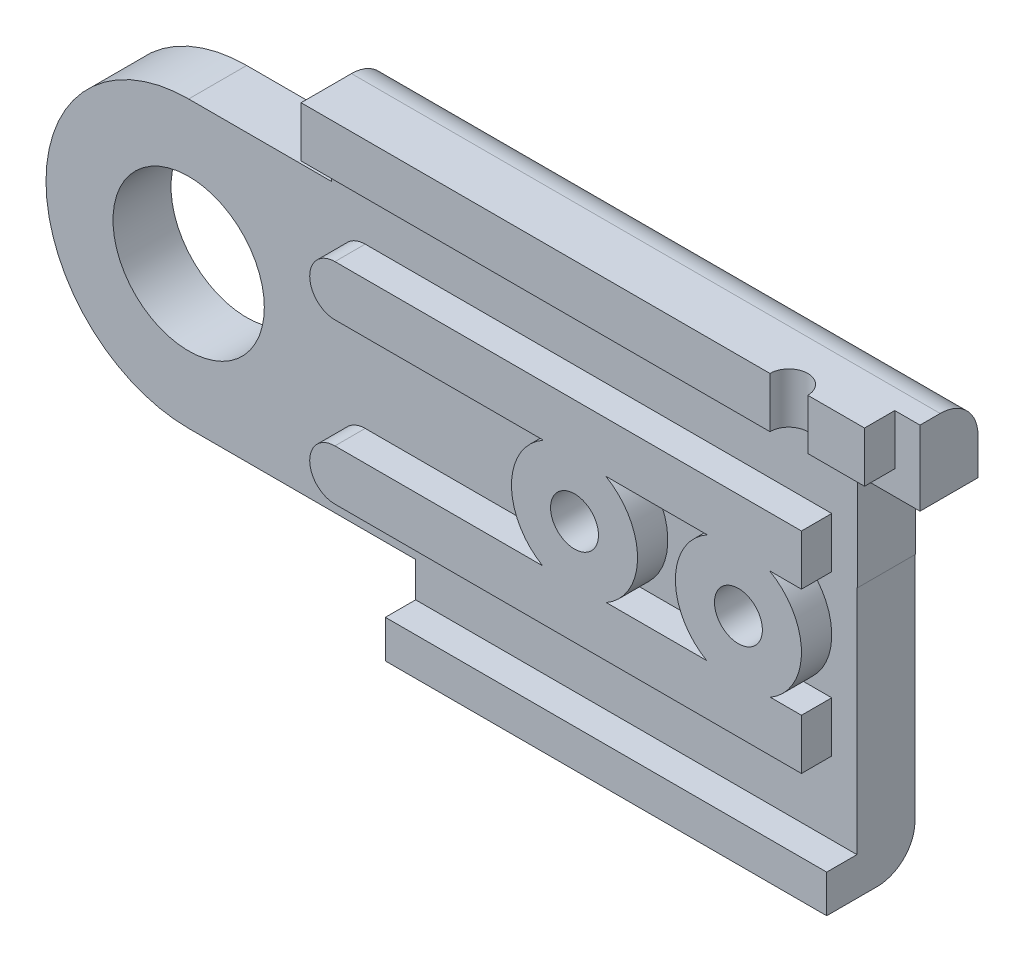
SolidWorks part; units mm, degrees
ref_plane "Front Plane" through (0, 0, 0) normal (0, 0, 1) x (1, 0, 0)
ref_plane "Top Plane" through (0, 0, 0) normal (0, 1, 0) x (1, 0, 0)
ref_plane "Right Plane" through (0, 0, 0) normal (1, 0, 0) x (0, 0, -1)
sketch "Sketch3" plane through (0, 0, 0) normal (0, 0, 1) x (1, 0, 0)
  line L7 (8, 0) -> (9, -2.5431)
  line L11 (35, 6.9569) -> (32, 7.4569)
  line L18 (5.6569, 5.6569) -> (5.6569, 7.4569)
  line L19 (5.6569, 7.4569) -> (32, 7.4569)
  line L20 (26.5, -7.0431) -> (9, -7.0431)
  line L21 (9, -7.0431) -> (9, -2.5431)
  line L23 (30.0502, -4.9929) -> (26.5, -7.0431)
  arc A4 (8, 0) -> (5.6569, 5.6569) centre (0, 0) ccw
  arc A5 (30.0502, -4.9929) -> (35, 6.9569) centre (35, -0.0431) ccw
  dimension "D3" = 3.5503
  dimension "D10" = 2.5431
  dimension "D17" = 14
  dimension "D4" = 5.6569
  dimension "D5" = 135
  dimension "D2" = 35
  dimension "D6" = 14.5
  dimension "D7" = 4.5
  dimension "D8" = 1
  dimension "D9" = 45
  dimension "D11" = 1.8
  dimension "D14" = 3
extrude "Boss-Extrude1" add sketch "Sketch3" along normal blind 2 contours A5 L11 L19 L18 A4 L7 L21 L20 L23
sketch "Sketch20" plane through (0, 0, 0) normal (0, 0, 1) x (1, 0, 0)
  line L0 (0, 7) -> (0, 7.5) construction
  line L1 (0, 7.5) -> (-19.4737, 7.5) construction
  line L2 (0, 5.3) -> (-14, 5.3) construction
  line L3 (0, 4) -> (-14, 4) construction
  line L4 (-14, 4) -> (-14, 5.3) construction
  line L5 (0, 5.3) -> (17.4849, 5.3) construction
  line L6 (17.4849, 5.3) -> (17.4849, 4) construction
  line L7 (17.4849, 4) -> (0, 4) construction
  line L8 (-2.5, 7.5) -> (-2.5, 2.868) construction
  circle A0 centre (0, 0) radius 7 construction
  circle A1 centre (0, 0) radius 3.9 construction
  circle A3 centre (0, 0) radius 5.3 construction
  circle A4 centre (0, 0) radius 4 construction
  circle A5 centre (0, 0) radius 2 construction
  dimension "D1" = 0
  dimension "D2" = 2.5
ref_plane "Plane1" through (0, 0, 2) normal (0, 0, 1) x (1, 0, 0)
sketch "Sketch4" plane through (0, 0, 2) normal (0, 0, 1) x (1, 0, 0)
  line L4 (5.6569, 5.6569) -> (5.6569, 7.5)
  line L5 (5.6569, 5.6569) -> (5.6569, 7.4569) construction
  line L6 (5.6569, 7.5) -> (26.5, 7.5)
  line L10 (8, 0) -> (9, -2.5431)
  line L11 (9, -2.5431) -> (9, -7.0431)
  line L12 (9, -7.0431) -> (26.5, -7.0431)
  line L13 (26.5, -7.0431) -> (26.5, 7.5)
  arc A0 (8, 0) -> (5.6569, 5.6569) centre (0, 0) ccw construction
  arc A3 (8, 0) -> (5.6569, 5.6569) centre (0, 0) ccw
sketch "Sketch22" plane through (0, 0, 2) normal (0, 0, 1) x (1, 0, 0)
  line L1 (5.6569, 7.4569) -> (26.5, 7.4569)
  line L6 (8, 0) -> (9, -2.5431)
  line L7 (9, -2.5431) -> (9, -7.0431)
  line L8 (9, -7.0431) -> (26.5, -7.0431)
  line L10 (26.5, 7.4569) -> (32, 7.4569)
  line L11 (32, 7.4569) -> (32, 2.1289)
  line L12 (32, 2.1289) -> (28.2751, 2.1289)
  line L13 (26.5, -7.0431) -> (28.2751, -6.018)
  line L14 (30.0502, -4.9929) -> (26.5, -7.0431) construction
  line L15 (28.2751, -6.018) -> (28.2751, 2.1289)
  line L16 (5.6569, 7.4569) -> (5.6569, 5.6569)
  arc A0 (8, 0) -> (5.6569, 5.6569) centre (0, 0) ccw
  dimension "D1" = 5.328
extrude "Boss-Extrude6" add sketch "Sketch22" along normal blind 4.5
sketch "Sketch25" plane through (0, 0, 2) normal (0, 0, 1) x (1, 0, 0)
  line L0 (0, 5.3) -> (18.0981, 5.3) construction
  line L1 (0, 4) -> (18.0981, 4) construction
  line L2 (18.0981, 4) -> (18.0981, 5.3) construction
sketch "Sketch26" plane through (0, 0, 2) normal (0, 0, 1) x (1, 0, 0)
  line L1 (18.0981, 5.3) -> (2.5301, 5.3)
  line L2 (18.0981, 4) -> (2.5301, 4)
  line L3 (2.5301, 5.3) -> (2.5301, 4)
  line L4 (18.0981, 5.3) -> (32, 5.3)
  line L5 (32, 2.1289) -> (32, 7.4569) construction
  line L6 (32, 5.3) -> (32, 4)
  line L7 (32, 4) -> (18.0981, 4)
extrude "Cut-Extrude6" cut sketch "Sketch26" along normal blind 4.5
ref_plane "Plane18" through (0, 0, 6.5) normal (0, 0, 1) x (1, 0, 0)
sketch "Sketch31" plane through (0, 0, 6.5) normal (0, 0, 1) x (1, 0, 0)
  line L0 (2.4327, 5.6569) -> (0, 5.6569)
  line L4 (9, -5.6569) -> (0, -5.6569)
  line L7 (2.4327, 5.6569) -> (5.6569, 5.6569)
  line L8 (5.6569, 5.6569) -> (5.6569, 7.4569)
  line L12 (9, -7.0431) -> (9, -5.6569)
  line L13 (9, -2.5431) -> (9, -7.0431) construction
  line L16 (32, 7.4569) -> (32, 2.1289)
  line L17 (32, 2.1289) -> (28.2751, 2.1289)
  line L22 (5.6569, 7.4569) -> (5.6569, 8.9569)
  line L23 (5.6569, 8.9569) -> (32, 8.9569)
  line L24 (32, 8.9569) -> (32, 7.4569)
  line L25 (9, -7.0431) -> (9, -8.5431)
  line L26 (9, -8.5431) -> (26.5, -8.5431)
  line L27 (26.5, -8.5431) -> (26.5, -7.0431)
  line L28 (26.5, -7.0431) -> (26.5, 2.1289)
  line L29 (26.5, 2.1289) -> (28.2751, 2.1289)
  line L30 (9, -7.0431) -> (26.5, -7.0431) construction
  line L31 (32, 7.4569) -> (5.6569, 7.4569) construction
  arc A0 (0, 5.6569) -> (0, -5.6569) centre (0, 0) ccw
  dimension "D1" = 5.6569
  dimension "D2" = 5.6569
  dimension "D3" = 1.5
  dimension "D4" = 1.5
extrude "Boss-Extrude14" add sketch "Sketch31" along normal blind 2.3 separate body
sketch "Sketch32" plane through (0, 0, 8.8) normal (0, 0, 1) x (1, 0, 0)
  circle A0 centre (0, 0) radius 3
  dimension "D1" = 6
extrude "Cut-Extrude7" cut sketch "Sketch32" against normal blind 2.3
sketch "Sketch33" plane through (0, 0, 8.8) normal (0, 0, 1) x (1, 0, 0)
  line L1 (5.6569, 8.9569) -> (5.6569, 6.9569)
  line L4 (9, -7.0431) -> (9, -8.5431)
  line L7 (7, -4.1569) -> (25.5, -4.1569)
  line L11 (9, -8.5431) -> (26.5, -8.5431)
  line L15 (26.5, -8.5431) -> (26.5, -7.0431)
  line L16 (26.5, -7.0431) -> (9, -7.0431)
  line L17 (5.6569, 8.9569) -> (28, 8.9569)
  line L18 (32, 8.9569) -> (5.6569, 8.9569) construction
  line L21 (28, 6.9569) -> (28, 8.9569)
  line L22 (25.5, -4.1569) -> (25.5, -2.1569)
  line L23 (25.5, -2.1569) -> (7, -2.1569)
  line L27 (5.6569, 6.9569) -> (28, 6.9569)
  line L28 (25.5, 2.172) -> (7, 2.172)
  line L30 (7, 4.172) -> (25.5, 4.172)
  line L33 (25.5, 2.172) -> (25.5, 4.172)
  line L34 (32, 2.1289) -> (32, 8.9569) construction
  line L35 (9, -8.5431) -> (26.5, -8.5431) construction
  line L37 (26.5, -8.5431) -> (26.5, 2.1289) construction
  arc A1 (7, -2.1569) -> (7, -4.1569) centre (7, -3.1569) ccw
  arc A2 (7, 4.172) -> (7, 2.172) centre (7, 3.172) ccw
  dimension "D1" = 1.5
  dimension "D2" = 2
  dimension "D3" = 2
  dimension "D5" = 2
  dimension "D6" = 2.5
  dimension "D8" = 4
extrude "Boss-Extrude15" add sketch "Sketch33" along normal blind 1.2
sketch "Sketch34" plane through (0, 0, 2) normal (0, 0, 1) x (1, 0, 0)
  line L0 (35, 5.3) -> (18.0981, 5.3) construction
  line L1 (35, 4) -> (18.0981, 4) construction
  circle A0 centre (35, -0.0431) radius 2 construction
  circle A1 centre (35, -0.0431) radius 5.3431 construction
  circle A2 centre (35, -0.0431) radius 4.0431 construction
sketch "Sketch35" plane through (0, 0, 8.8) normal (0, 0, 1) x (1, 0, 0)
  line L0 (32, 2.1289) -> (32, 6)
  line L1 (32, 2.1289) -> (26.5203, 2.1289)
  line L2 (32, 6) -> (26.5203, 6)
  line L3 (26.5203, 2.1289) -> (26.5203, 6)
  line L4 (32, 2.1289) -> (32, 8.9569) construction
  dimension "D1" = 5.4796
extrude "Cut-Extrude8" cut sketch "Sketch35" against normal blind 2.4
sketch "Sketch36" plane through (0, 0, 6.4) normal (0, 0, 1) x (1, 0, 0)
  line L0 (32, 2.1289) -> (32, 4)
  line L1 (32, 2.1289) -> (28.3, 2.1289)
  line L2 (32, 4) -> (28.3, 4)
  line L3 (28.3, 2.1289) -> (28.3, 4)
  line L4 (26.5, -7.0431) -> (26.5, 7.5) construction
  dimension "D1" = 1.8
extrude "Cut-Extrude9" cut sketch "Sketch36" against normal blind 4.4
sketch "Sketch37" plane through (0, 0, 2) normal (0, 0, 1) x (1, 0, 0)
  circle A0 centre (35, -0.0431) radius 3.9
  dimension "D1" = 7.8
extrude "Boss-Extrude16" add sketch "Sketch37" along normal blind 4.4
sketch "Sketch39" plane through (0, 0, 6.4) normal (0, 0, 1) x (1, 0, 0)
  line L0 (34, 0.9367) -> (34, -1.0229)
  arc A0 (34, -1.0229) -> (34, 0.9367) centre (35, -0.0431) ccw
  dimension "D2" = 2.8
  dimension "D1" = 1
extrude "Cut-Extrude10" cut sketch "Sketch39" against normal through all
sketch "Sketch43" plane through (0, 0, 8.8) normal (0, 0, 1) x (1, 0, 0)
  line L2 (0, -5.6569) -> (9, -5.6569) construction
  circle A0 centre (16.5, 0) radius 2.5
  circle A1 centre (23, 0) radius 2.5
  dimension "D1" = 7.5
  dimension "D3" = 5
  dimension "D4" = 6.5
  dimension "D2" = 5.6569
extrude "Boss-Extrude17" add sketch "Sketch43" along normal blind 1.2
sketch "Sketch44" plane through (0, 0, 10) normal (0, 0, 1) x (1, 0, 0)
  circle A0 centre (16.5, 0) radius 0.95
  circle A1 centre (23, 0) radius 0.95
  dimension "D1" = 1.9
  dimension "D2" = 1.9
extrude "Cut-Extrude11" cut sketch "Sketch44" against normal through all
sketch "Sketch45" plane through (0, 0, 0) normal (0, 0, -1) x (-1, 0, 0)
  circle A0 centre (-16.5, 0) radius 2
  circle A1 centre (-23, 0) radius 2
extrude "Cut-Extrude12" cut sketch "Sketch45" against normal blind 4.5
ref_plane "Plane17" through (0, 0, 10) normal (0, 0, 1) x (1, 0, 0)
sketch "Sketch48" plane through (0, 0, 2) normal (0, 0, 1) x (1, 0, 0)
  circle A0 centre (35, -0.0431) radius 6 construction
  dimension "D1" = 12
sketch "Sketch49" plane through (0, 6.9569, 0) normal (0, -1, 0) x (1, 0, 0)
  line L0 (5.6569, 10) -> (28, 10) construction
  line L1 (28, 10) -> (28, 8.8) construction
  line L2 (5.6569, 10) -> (5.6569, 8.8) construction
  circle A0 centre (25, 10) radius 0.75
  dimension "D1" = 3
  dimension "D3" = 1.5
  dimension "D2" = 19.3431
sketch "Sketch50" plane through (0, 0, 10) normal (0, 0, 1) x (1, 0, 0)
  line L0 (25, 6.9569) -> (27.3935, -5.0795) construction
extrude "Cut-Extrude13" cut sketch "Sketch49" against normal blind 3
sketch "Sketch51" plane through (0, 0, 8.8) normal (0, 0, 1) x (1, 0, 0)
  line L0 (32, 8.9569) -> (29, 8.9569)
  line L1 (32, 8.9569) -> (32, 4.9913)
  line L2 (29, 8.9569) -> (29, 4.9913)
  line L3 (32, 4.9913) -> (29, 4.9913)
  line L5 (32, 8.9569) -> (28, 8.9569) construction
  line L7 (32, 6) -> (32, 8.9569) construction
  dimension "D1" = 3
extrude "Cut-Extrude14" cut sketch "Sketch51" against normal blind 6.8
fillet "Fillet1" radius 1.5 2 edges at (17.3284, 8.9569, 6.5) (17.75, -8.5431, 6.5)
fillet "Fillet3" radius 1 6 edges at (28.2751, -6.018, 4.25) (29, 7.4569, 4.25) (9, -7.0431, 3.25) (5.6569, 7.4569, 3.25) (17.75, -7.0431, 0) (18.8284, 7.4569, 0)
split "Split1" trim tools "Plane18" bodies to split 141 139 resulting bodies 143 144
delete or keep bodies "Body-Delete/Keep 1" type delete bodies bodies 144
